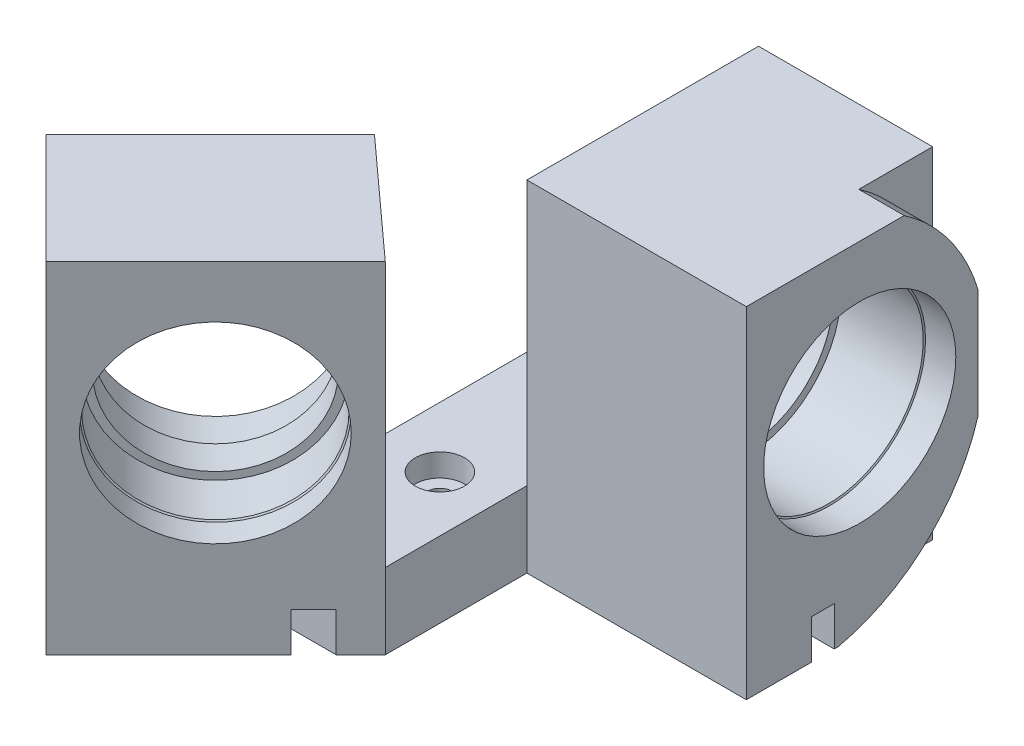
SolidWorks part; units mm, degrees
material "6061-T6 (SS)"
ref_plane "Front Plane" through (0, 0, 0) normal (0, 0, 1) x (1, 0, 0)
ref_plane "Top Plane" through (0, 0, 0) normal (0, 1, 0) x (1, 0, 0)
ref_plane "Right Plane" through (0, 0, 0) normal (1, 0, 0) x (0, 0, -1)
sketch "Sketch1" plane through (0, 0, 0) normal (0, 1, 0) x (1, 0, 0)
  line L0 (5.3197, 25.3427) -> (-23.6894, 25.3427)
  line L1 (-23.6894, 25.3427) -> (-23.6894, 6.6264)
  line L2 (-23.6894, 6.6264) -> (-46.1111, -15.7953)
  line L3 (-46.1111, -15.7953) -> (-60.6955, -1.2109)
  line L4 (-60.6955, -1.2109) -> (-38.989, 20.4956)
  line L5 (-38.989, 20.4956) -> (-38.989, 55.9623)
  line L6 (-38.989, 55.9623) -> (5.3197, 55.9623)
  line L7 (5.3197, 55.9623) -> (5.3197, 25.3427)
extrude "Boss-Extrude1" add sketch "Sketch1" along normal blind 45
ref_plane "Plane1" through (0, 25.4, 0) normal (0, -1, 0) x (-1, 0, 0)
sketch "Sketch2" plane through (-15.1579, 0, -15.1579) normal (0.7071, 0, 0.7071) x (0.7071, 0, -0.7071)
  circle A0 centre (-27.942, 25.4) radius 12.5
extrude "Cut-Extrude1" cut sketch "Sketch2" against normal blind 10
sketch "Sketch3" plane through (5.3197, 0, 0) normal (1, 0, 0) x (0, 0, -1)
  circle A0 centre (40.3279, 25.4) radius 12.5081
extrude "Cut-Extrude2" cut sketch "Sketch3" against normal blind 15
sketch "Sketch4" plane through (-22.2289, 0, -22.2289) normal (0.7071, 0, 0.7071) x (0.7071, 0, -0.7071)
  circle A0 centre (-27.942, 25.4) radius 11.5
  dimension "D1" = 23
extrude "Cut-Extrude3" cut sketch "Sketch4" against normal up to next
sketch "Sketch5" plane through (-9.6803, 0, 0) normal (1, 0, 0) x (0, 0, -1)
  circle A0 centre (40.3279, 25.4) radius 11.5
  dimension "D1" = 23
extrude "Cut-Extrude4" cut sketch "Sketch5" against normal up to next
hole_wizard "SM1 Tapped Hole1" positions "Sketch6" profile "Sketch7" tap size "SM1" standard "UNS"
sketch "Sketch6" plane through (5.3197, 0, 0) normal (1, 0, 0) x (0, 0, -1)
  point P0 (40.3279, 25.4)
sketch "Sketch7" plane through (5.3197, 25.4, -40.3279) normal (0, 1, 0) x (0, 0, -1)
  line L0 (0, 0) -> (0, 11.6309)
  line L1 (0, 11.6309) -> (12.7, 4)
  line L2 (12.7, 4) -> (12.7, 0)
  line L5 (12.7, 0) -> (0, 0)
  line L10 (0, 11.6309) -> (-12.7, 4) construction
  line L11 (0, -6.35) -> (0, 107.95) construction
  dimension "Tap Drill Dia." = 25.4
  dimension "Tap Drill Depth" = 4
  dimension "Drill Angle" = 118
cosmetic thread "Hole Thread1" parameters "D1"=4, "D2"=26.289
hole_wizard "SM1 Tapped Hole2" positions "Sketch8" profile "Sketch9" tap size "SM1" standard "UNS"
sketch "Sketch8" plane through (-15.1579, 0, -15.1579) normal (0.7071, 0, 0.7071) x (0.7071, 0, -0.7071)
  point P0 (-27.942, 25.4)
sketch "Sketch9" plane through (-34.9159, 25.4, 4.6001) normal (0, 1, 0) x (0.7071, 0, -0.7071)
  line L0 (0, 0) -> (0, 11.1309)
  line L1 (0, 11.1309) -> (12.7, 3.5)
  line L2 (12.7, 3.5) -> (12.7, 0)
  line L5 (12.7, 0) -> (0, 0)
  line L10 (0, 11.1309) -> (-12.7, 3.5) construction
  line L11 (0, -6.35) -> (0, 107.95) construction
  dimension "Tap Drill Dia." = 25.4
  dimension "Tap Drill Depth" = 3.5
  dimension "Drill Angle" = 118
cosmetic thread "Hole Thread2" parameters "D1"=3.5, "D2"=26.289
sketch "Sketch11" plane through (0, 45, 0) normal (0, 1, 0) x (1, 0, 0)
  line L0 (-23.6894, 6.6264) -> (-38.989, 20.4956)
  line L1 (-38.989, 20.4956) -> (-38.989, 55.9623)
  line L2 (-38.989, 55.9623) -> (-23.6894, 55.9623)
  line L3 (-38.989, 55.9623) -> (5.3197, 55.9623) construction
  line L4 (-23.6894, 55.9623) -> (-23.6894, 6.6264)
extrude "Cut-Extrude5" cut sketch "Sketch11" against normal blind 35
hole_wizard "SM1 Tapped Hole3" positions "Sketch12" profile "Sketch13" tap size "SM1" standard "UNS"
sketch "Sketch12" plane through (-23.6894, 0, 0) normal (-1, 0, 0) x (0, 0, 1)
  point P0 (-40.3279, 25.4)
sketch "Sketch13" plane through (-23.6894, 25.4, -40.3279) normal (0, 1, 0) x (0, 0, 1)
  line L0 (0, 0) -> (0, 13.0409)
  line L1 (0, 13.0409) -> (12.7, 5.41)
  line L2 (12.7, 5.41) -> (12.7, 0)
  line L5 (12.7, 0) -> (0, 0)
  line L10 (0, 13.0409) -> (-12.7, 5.41) construction
  line L11 (0, -6.35) -> (0, 107.95) construction
  dimension "Tap Drill Dia." = 25.4
  dimension "Tap Drill Depth" = 5.41
  dimension "Drill Angle" = 118
cosmetic thread "Hole Thread3" parameters "D1"=5.41, "D2"=26.289
hole_wizard "SM1 Tapped Hole4" positions "Sketch14" profile "Sketch15" tap size "SM1" standard "UNS"
sketch "Sketch14" plane through (-29.7423, 0, -29.7423) normal (-0.7071, 0, -0.7071) x (-0.7071, 0, 0.7071)
  point P0 (27.942, 25.4)
sketch "Sketch15" plane through (-49.5003, 25.4, -9.9843) normal (0, 1, 0) x (-0.7071, 0, 0.7071)
  line L0 (0, 0) -> (0, 13.0409)
  line L1 (0, 13.0409) -> (12.7, 5.41)
  line L2 (12.7, 5.41) -> (12.7, 0)
  line L5 (12.7, 0) -> (0, 0)
  line L10 (0, 13.0409) -> (-12.7, 5.41) construction
  line L11 (0, -6.35) -> (0, 107.95) construction
  dimension "Tap Drill Dia." = 25.4
  dimension "Tap Drill Depth" = 5.41
  dimension "Drill Angle" = 118
cosmetic thread "Hole Thread4" parameters "D1"=5.41, "D2"=26.289
hole_wizard "CBORE for M3 SHCS1" positions "Sketch16" profile "Sketch17" counterbore size "M3" standard "ANSI Metric" end condition up to next
sketch "Sketch16" plane through (0, 10, 0) normal (0, 1, 0) x (1, 0, 0)
  point P0 (-31.0157, 48.4337)
  point P2 (-31.0157, 21.1714)
sketch "Sketch17" plane through (-31.0157, 10, -48.4337) normal (1, 0, 0) x (0, 0, 1)
  line L0 (0, 0) -> (0, 10)
  line L1 (0, 10) -> (1.6, 10)
  line L3 (1.6, 10) -> (1.6, 3)
  line L4 (1.6, 3) -> (3.25, 3)
  line L5 (3.25, 3) -> (3.25, 0)
  line L7 (3.25, 0) -> (0, 0)
  line L11 (0, -6.35) -> (0, 107.95) construction
  dimension "Thru Hole Dia." = 3.2
  dimension "Thru Hole Depth" = 10
  dimension "C'Bore Dia." = 6.5
  dimension "C'Bore Depth" = 3
ref_plane "Plane2" through (-0.0195, 0, 0) normal (-1, 0, 0) x (0, 0, 1)
sketch "Sketch18" plane through (-0.0195, 0, 0) normal (-1, 0, 0) x (0, 0, 1)
  line L11 (-46.2048, 45) -> (-56.7668, 45)
  line L13 (-56.7668, 45) -> (-56.7668, 28.0868)
  line L15 (-56.6196, 19.8341) -> (-56.6196, 0)
  line L16 (-56.6196, 0) -> (-37.4844, 0)
  line L18 (-55.9623, 45) -> (-55.9623, 0) construction
  line L19 (-20.4956, 0) -> (-55.9623, 0) construction
  line L24 (-25.3427, 45) -> (-55.9623, 45) construction
  arc A0 (-56.6196, 19.8341) -> (-37.4844, 0) centre (-32.0401, 24.4) ccw
  arc A1 (-46.2048, 45) -> (-56.7668, 28.0868) centre (-32.0401, 24.4) ccw
  dimension "D5" = 50
  dimension "D6" = 23.9222
  dimension "D7" = 24.4
extrude "Cut-Extrude6" cut sketch "Sketch18" along normal blind 6 from surface at -5.3392 starting at face at (5.3197, 25.4, -53.0279)
hole_wizard "Ø3.0mm Dowel Hole1" positions "Sketch19" profile "Sketch20" hole size "Ø3.0" standard "ANSI Metric"
sketch "Sketch19" plane through (0, 0, 0) normal (0, -1, 0) x (-1, 0, 0)
  line L0 (46.1111, -15.7953) -> (60.6955, -1.2109) construction
  line L1 (23.6894, 6.6264) -> (46.1111, -15.7953) construction
  line L2 (38.989, 55.9623) -> (-5.3197, 55.9623) construction
  line L3 (38.989, 20.4956) -> (38.989, 55.9623) construction
  point P0 (42.5756, 1.8823)
  point P2 (30.989, 35.4623)
  dimension "D1" = 15
  dimension "D2" = 10
  dimension "D3" = 20.5
  dimension "D4" = 8
sketch "Sketch20" plane through (-42.5756, 0, -1.8823) normal (1, 0, 0) x (0, 0, -1)
  line L0 (0, 0) -> (0, 6.1013)
  line L1 (0, 6.1013) -> (1.5, 5.2)
  line L2 (1.5, 5.2) -> (1.5, 0)
  line L5 (1.5, 0) -> (0, 0)
  line L10 (0, 6.1013) -> (-1.5, 5.2) construction
  line L11 (0, -6.35) -> (0, 107.95) construction
  dimension "Hole Dia." = 3
  dimension "Hole Depth" = 5.2
  dimension "Drill Angle" = 118
sketch "Sketch21" plane through (0, 0, 0) normal (0, -1, 0) x (1, 0, 0)
  line L1 (-42.5756, -0.3823) -> (-25.1242, -0.3823)
  line L2 (-42.5756, -0.3823) -> (-42.5756, -3.3823)
  line L3 (-42.5756, -3.3823) -> (-25.1242, -3.3823)
  line L4 (-25.1242, -0.3823) -> (-25.1242, -3.3823)
  line L5 (-42.5756, -0.3823) -> (-25.1242, -3.3823) construction
  line L6 (-42.5756, -3.3823) -> (-25.1242, -0.3823) construction
  line L7 (-30.989, -33.9623) -> (6.1531, -33.9623)
  line L8 (-30.989, -33.9623) -> (-30.989, -36.9623)
  line L9 (-30.989, -36.9623) -> (6.1531, -36.9623)
  line L10 (6.1531, -33.9623) -> (6.1531, -36.9623)
  line L11 (-30.989, -33.9623) -> (6.1531, -36.9623) construction
  line L12 (-30.989, -36.9623) -> (6.1531, -33.9623) construction
  circle A0 centre (-42.5756, -1.8823) radius 1.5 construction
  circle A1 centre (-42.5756, -1.8823) radius 1.5 construction
  circle A2 centre (-30.989, -35.4623) radius 1.5 construction
  circle A3 centre (-30.989, -35.4623) radius 1.5 construction
  point P4 (-33.8499, -1.8823)
  point P13 (-12.418, -35.4623)
extrude "Cut-Extrude7" cut sketch "Sketch21" against normal blind 5.2
